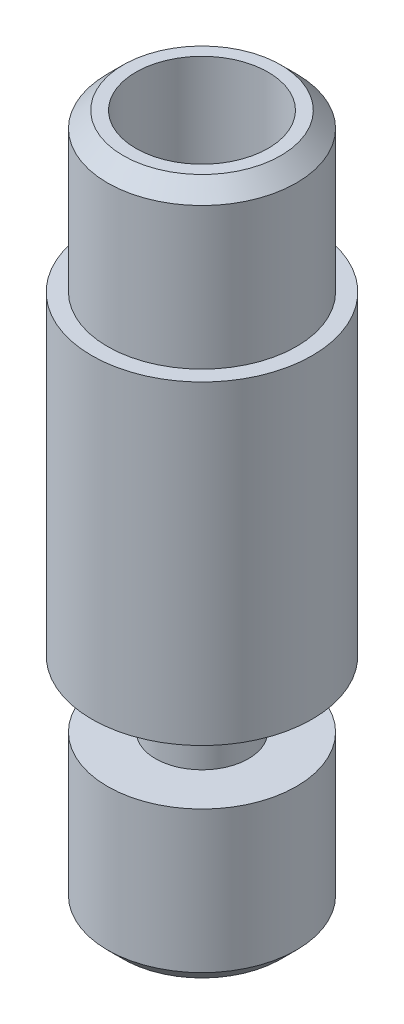
SolidWorks part; units mm, degrees
material "AISI 304"
ref_plane "Front Plane" through (0, 0, 0) normal (0, 0, 1) x (1, 0, 0)
ref_plane "Top Plane" through (0, 0, 0) normal (0, 1, 0) x (1, 0, 0)
ref_plane "Right Plane" through (0, 0, 0) normal (1, 0, 0) x (0, 0, -1)
sketch "Sketch1" plane through (0, 0, 0) normal (0, 0, 1) x (1, 0, 0)
  line L0 (0, 0) -> (0, 15) construction
  line L1 (1.475, 0) -> (3.5, 0)
  line L2 (3.5, 0) -> (3.5, 10)
  line L3 (3.5, 10) -> (3, 10)
  line L4 (3, 10) -> (3, 15)
  line L5 (3, 15) -> (0, 15)
  line L6 (0, -7.1) -> (0, 15)
  line L7 (0, -7.1) -> (3, -7.1)
  line L8 (3, -7.1) -> (3, -2.1)
  line L9 (3, -2.1) -> (1.475, -2.1)
  line L10 (1.475, -2.1) -> (1.475, 0)
  dimension "D1" = 6
  dimension "D2" = 2.95
  dimension "D3" = 7
  dimension "D4" = 15
  dimension "D5" = 2.1
  dimension "D6" = 5
  dimension "D7" = 5
  dimension "D8" = 0.5
revolve "Revolve1" add sketch "Sketch1" angle 360 about L0
sketch "Sketch2" plane through (0, 0, 0) normal (0, 0, 1) x (1, 0, 0)
  line L0 (0, 15) -> (0, -7.1) construction
  line L1 (3, 15) -> (-3, 15) construction
  line L2 (-3, -7.1) -> (3, -7.1) construction
  line L3 (0, 15) -> (2.1, 15)
  line L4 (2.1, 15) -> (2.1, 10)
  line L5 (3.5, 10) -> (-3.5, 10) construction
  line L6 (2.1, 10) -> (1, 9.3391)
  line L7 (1, 9.3391) -> (1, -7.1)
  line L8 (1, -7.1) -> (0, -7.1)
  line L9 (0, 15) -> (0, -7.1)
  dimension "D1" = 2
  dimension "D2" = 4.2
  dimension "D3" = 59
revolve "Cut-Revolve1" cut sketch "Sketch2" angle 360 about L0
chamfer "Chamfer1" distance 0.5 angle 45 2 edges at (0, -7.1, -3) (0, 15, -3)
